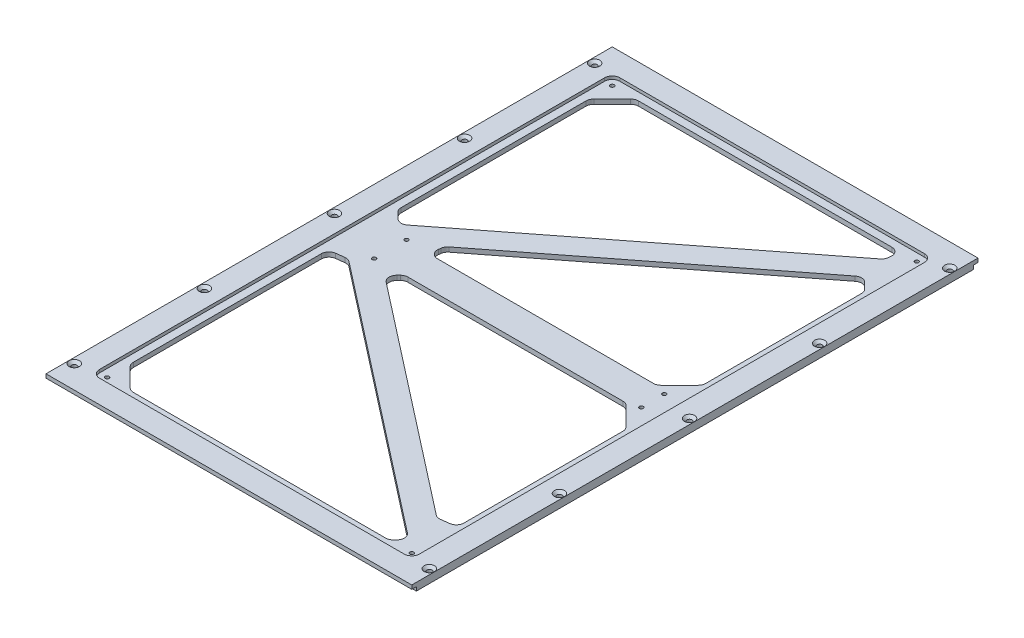
SolidWorks part; units mm, degrees
material "2014 Alloy"
ref_plane "Front Plane" through (0, 0, 0) normal (0, 0, 1) x (1, 0, 0)
ref_plane "Top Plane" through (0, 0, 0) normal (0, 1, 0) x (1, 0, 0)
ref_plane "Right Plane" through (0, 0, 0) normal (1, 0, 0) x (0, 0, -1)
sketch "Sketch1" plane through (0, 0, 0) normal (0, 1, 0) x (1, 0, 0)
  line L1 (0, 0) -> (-239, 0)
  line L2 (0, 0) -> (0, 370)
  line L3 (0, 370) -> (-239, 370)
  line L4 (-239, 0) -> (-239, 370)
  dimension "D1" = 239
  dimension "D2" = 370
extrude "Boss-Extrude1" add sketch "Sketch1" along normal blind 5
hole_wizard "CSK for M3 Hex Socket Countersunk Cap Screw1" positions "Sketch3" profile "Sketch2" countersink size "M3" standard "ISO" end condition through all
sketch "Sketch3" plane through (0, 5, 0) normal (0, 1, 0) x (1, 0, 0)
  line L0 (-239, 185) -> (0, 185) construction
  line L1 (-239, 370) -> (-239, 0) construction
  line L2 (0, 0) -> (0, 370) construction
  point P0 (-3.5, 15)
  point P2 (-3.5, 100)
  point P4 (-3.5, 185)
  point P6 (-3.5, 270)
  point P8 (-3.5, 355)
  dimension "D1" = 85
  dimension "D2" = 85
  dimension "D3" = 85
  dimension "D4" = 85
  dimension "D5" = 3.5
sketch "Sketch2" plane through (-3.5, 5, -15) normal (1, 0, 0) x (0, 0, 1)
  line L0 (0, 0) -> (0, 5)
  line L1 (0, 5) -> (1.7, 5)
  line L2 (1.7, 5) -> (1.7, 1.66)
  line L3 (1.7, 1.66) -> (3.36, 0)
  line L5 (3.36, 0) -> (0, 0)
  line L6 (-1.7, 1.66) -> (-3.36, 0) construction
  line L11 (0, -6.35) -> (0, 107.95) construction
  dimension "Thru Hole Dia." = 3.4
  dimension "Thru Hole Depth" = 5
  dimension "Near C'Sink Dia." = 6.72
  dimension "Near C'Sink Angle" = 90
sketch "Sketch7" plane through (0, 5, 0) normal (0, 1, 0) x (1, 0, 0)
  line L0 (-119.5, 0) -> (-119.5, 370) construction
  line L1 (-239, 0) -> (0, 0) construction
  line L2 (0, 370) -> (-239, 370) construction
sketch "Sketch8" plane through (0, 0, 0) normal (0, 0, 1) x (1, 0, 0)
  line L0 (-119.5, 5) -> (-119.5, 0) construction
  line L1 (-239, 0) -> (0, 0) construction
ref_plane "Plane1" through (-119.5, 0, 0) normal (-1, 0, 0) x (0, 0, 1)
mirror "Mirror1" about plane through (-119.5, 0, 0) normal (-1, 0, 0) of "CSK for M3 Hex Socket Countersunk Cap Screw1"
sketch "Sketch12" plane through (0, 0, 0) normal (0, -1, 0) x (1, 0, 0)
  line L0 (-239, -370) -> (-239, 0) construction
  line L1 (0, 0) -> (-239, 0)
  line L2 (0, 0) -> (0, -3)
  line L3 (0, -3) -> (-239, -3)
  line L4 (-239, 0) -> (-239, -3)
  line L5 (0, 0) -> (0, -370) construction
  line L6 (-239, -370) -> (0, -370)
  line L7 (-239, -370) -> (-239, -367)
  line L8 (-239, -367) -> (0, -367)
  line L9 (0, -370) -> (0, -367)
  dimension "D1" = 3
  dimension "D2" = 3
extrude "Cut-Extrude7" cut sketch "Sketch12" against normal blind 2.5
sketch "Sketch13" plane through (0, 5, 0) normal (0, 1, 0) x (1, 0, 0)
  line L0 (-239, 185) -> (0, 185) construction
  line L1 (-20, 39.0132) -> (-20, 175)
  line L2 (-194.5895, 175) -> (-20, 175)
  line L3 (-20, 350) -> (-219, 350)
  line L4 (-219, 350) -> (-219, 195)
  line L5 (-239, 370) -> (-239, 0) construction
  line L6 (0, 0) -> (0, 370) construction
  line L7 (-219, 195) -> (-20, 350)
  line L8 (-20, 330.9868) -> (-20, 195)
  line L9 (-20, 330.9868) -> (-194.5895, 195)
  line L10 (-20, 39.0132) -> (-194.5895, 175)
  line L11 (-219, 20) -> (-219, 175)
  line L12 (-219, 175) -> (-20, 20)
  line L13 (-20, 20) -> (-219, 20)
  line L14 (-194.5895, 195) -> (-20, 195)
  line L15 (-239, 0) -> (0, 0) construction
  dimension "D1" = 10
  dimension "D2" = 20
  dimension "D3" = 20
  dimension "D4" = 20
  dimension "D5" = 15
extrude "Cut-Extrude8" cut sketch "Sketch13" against normal through all
chamfer "Chamfer1" distance 15 angle 45 12 edges at (-219, 2.5, -175) (-20, 2.5, -20) (-20, 2.5, -39.0132) (-194.5895, 2.5, -175) (-219, 2.5, -195) (-194.5895, 2.5, -195) (-20, 2.5, -330.9868) (-20, 2.5, -195) (-20, 2.5, -350) (-219, 2.5, -350) (-219, 2.5, -20) (-20, 2.5, -175)
fillet "Fillet1" radius 5 24 edges at (-204, 2.5, -20) (-219, 2.5, -35) (-28.4322, 2.5, -26.5678) (-35, 2.5, -20) (-219, 2.5, -164.3118) (-207.1661, 2.5, -165.7827) (-186.1573, 2.5, -168.4322) (-179.5895, 2.5, -175) (-31.8339, 2.5, -48.2306) (-20, 2.5, -49.7014) (-35, 2.5, -195) (-20, 2.5, -210) (-183.9013, 2.5, -195) (-182.7556, 2.5, -204.2173) (-210.5678, 2.5, -201.5678) (-219, 2.5, -210) (-219, 2.5, -335) (-204, 2.5, -350) (-30.6882, 2.5, -350) (-31.8339, 2.5, -340.7827) (-28.4322, 2.5, -324.419) (-20, 2.5, -315.9868) (-35, 2.5, -175) (-20, 2.5, -160)
sketch "Sketch14" plane through (0, 5, 0) normal (0, 1, 0) x (1, 0, 0)
  line L0 (-20, 54.1184) -> (-20, 157.9289) construction
  line L1 (-224, 15) -> (-15, 15)
  line L2 (-224, 15) -> (-224, 355)
  line L3 (-224, 355) -> (-15, 355)
  line L4 (-15, 15) -> (-15, 355)
  line L5 (-219, 332.9289) -> (-219, 212.0711) construction
  line L6 (-201.9289, 20) -> (-37.0711, 20) construction
  line L7 (-36.3482, 350) -> (-201.9289, 350) construction
  dimension "D1" = 5
  dimension "D2" = 5
  dimension "D3" = 5
  dimension "D4" = 5
extrude "Cut-Extrude9" cut sketch "Sketch14" against normal blind 2
fillet "Fillet2" radius 5 4 edges at (-224, 4, -15) (-15, 4, -15) (-15, 4, -355) (-224, 4, -355)
hole_wizard "M3 Tapped Hole1" positions "Sketch17" profile "Sketch16" tap size "M3" standard "ISO"
sketch "Sketch17" plane through (0, 3, 0) normal (0, 1, 0) x (1, 0, 0)
  line L0 (-27.5, 202.5) -> (-27.5, 167.5) construction
  line L1 (-33.5355, 196.4645) -> (-21.4645, 208.5355) construction
  line L2 (-21.4645, 161.4645) -> (-33.5355, 173.5355) construction
  line L4 (-199, 210.5779) -> (-199, 159.4221) construction
  line L5 (-207.0831, 204.282) -> (-33.4678, 339.51) construction
  line L6 (-32.8975, 30.0458) -> (-205.5322, 164.51) construction
  line L8 (-224, 350) -> (-224, 20) construction
  arc A0 (-219, 355) -> (-224, 350) centre (-219, 350) ccw construction
  arc A1 (-15, 350) -> (-20, 355) centre (-20, 350) ccw construction
  arc A2 (-20, 15) -> (-15, 20) centre (-20, 20) ccw construction
  arc A3 (-224, 20) -> (-219, 15) centre (-219, 20) ccw construction
  point P0 (-219, 350)
  point P2 (-20, 350)
  point P4 (-20, 20)
  point P6 (-27.5, 192.5)
  point P8 (-219, 20)
  point P11 (-27.5, 177.5)
  point P13 (-199, 195.5779)
  point P15 (-199, 174.4221)
  dimension "D1" = 10
  dimension "D2" = 10
  dimension "D3" = 25
  dimension "D4" = 15
  dimension "D5" = 15
sketch "Sketch16" plane through (-219, 3, -350) normal (1, 0, 0) x (0, 0, 1)
  line L0 (0, 0) -> (0, 15.7511)
  line L1 (0, 15.7511) -> (1.25, 15)
  line L2 (1.25, 15) -> (1.25, 0)
  line L5 (1.25, 0) -> (0, 0)
  line L10 (0, 15.7511) -> (-1.25, 15) construction
  line L11 (0, -6.35) -> (0, 107.95) construction
  dimension "Tap Drill Dia." = 2.5
  dimension "Tap Drill Depth" = 15
  dimension "Drill Angle" = 118
cosmetic thread "Hole Thread1" parameters "D1"=3, "D2"=3
cosmetic thread "Hole Thread2" parameters "D1"=3, "D2"=3
cosmetic thread "Hole Thread3" parameters "D1"=3, "D2"=3
cosmetic thread "Hole Thread4" parameters "D1"=3, "D2"=3
cosmetic thread "Hole Thread5" parameters "D1"=3, "D2"=3
cosmetic thread "Hole Thread6" parameters "D1"=3, "D2"=3
cosmetic thread "Hole Thread7" parameters "D1"=3, "D2"=3
cosmetic thread "Hole Thread8" parameters "D1"=3, "D2"=3
